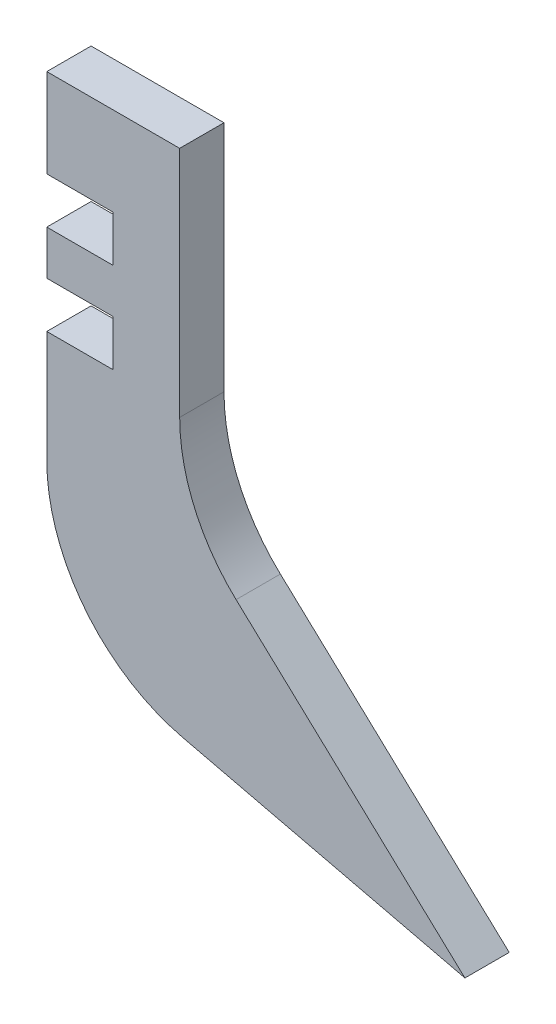
SolidWorks part; units mm, degrees
ref_plane "Front Plane" through (0, 0, 0) normal (0, 0, 1) x (1, 0, 0)
ref_plane "Top Plane" through (0, 0, 0) normal (0, 1, 0) x (1, 0, 0)
ref_plane "Right Plane" through (0, 0, 0) normal (1, 0, 0) x (0, 0, -1)
sketch "Sketch1" plane through (0, 0, 0) normal (0, 0, 1) x (1, 0, 0)
  line L0 (0, 53.7639) -> (0, 0)
  line L1 (0, 53.7639) -> (15, 53.7639)
  line L2 (15, 53.7639) -> (15, 18.7639)
  line L3 (0, 0) -> (47.1933, -11.2361)
  line L4 (15, 18.7639) -> (47.1933, -11.2361)
  point P3 (51.746, -38.2732)
  point P7 (42.9315, -17.7166)
  point P8 (15, 17.5048)
  point P9 (47.1933, -11.2361)
  dimension "D1" = 35
  dimension "D2" = 15
  dimension "D3" = 30
extrude "Boss-Extrude1" add sketch "Sketch1" along normal blind 5
fillet "Fillet1" radius 20 1 edges at (0, 0, 2.5)
fillet "Fillet2" radius 20 1 edges at (15, 18.7639, 2.5)
sketch "Sketch3" plane through (0, 0, 0) normal (0, 0, 1) x (1, 0, 0)
  line L0 (0, 53.7639) -> (0, 15.7973) construction
  line L1 (0, 43.7639) -> (7.5, 43.7639)
  line L2 (0, 43.7639) -> (0, 38.5639)
  line L3 (0, 38.5639) -> (7.5, 38.5639)
  line L4 (7.5, 43.7639) -> (7.5, 38.5639)
  line L6 (15, 53.7639) -> (0, 53.7639) construction
  line L8 (0, 33.5639) -> (7.5, 33.5639)
  line L9 (0, 33.5639) -> (0, 28.3639)
  line L10 (0, 28.3639) -> (7.5, 28.3639)
  line L11 (7.5, 33.5639) -> (7.5, 28.3639)
  dimension "D1" = 7.5
  dimension "D2" = 5.2
  dimension "D3" = 10
  dimension "D4" = 5.2
  dimension "D5" = 7.5
  dimension "D6" = 5
extrude "Cut-Extrude2" cut sketch "Sketch3" along normal blind 5
